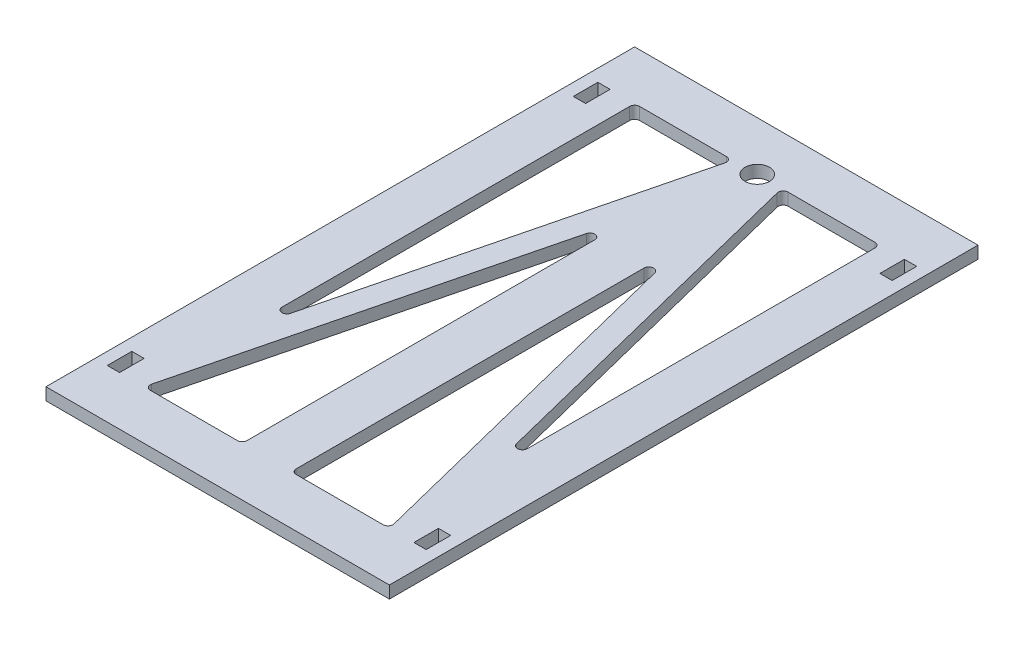
SolidWorks part; units mm, degrees
material "Beech"
ref_plane "Front Plane" through (0, 0, 0) normal (0, 0, 1) x (1, 0, 0)
ref_plane "Top Plane" through (0, 0, 0) normal (0, 1, 0) x (1, 0, 0)
ref_plane "Right Plane" through (0, 0, 0) normal (1, 0, 0) x (0, 0, -1)
sketch "Sketch1" plane through (0, 0, 0) normal (0, 1, 0) x (1, 0, 0)
  line L0 (0, 0) -> (177.8, 0)
  line L1 (0, 0) -> (0, 304.8)
  line L2 (177.8, 0) -> (177.8, 304.8)
  line L3 (0, 304.8) -> (177.8, 304.8)
  line L4 (0, 0) -> (12.7, 0)
  line L5 (0, 0) -> (0, -6.35)
  line L8 (177.8, 0) -> (165.1, 0)
  line L12 (127, 0) -> (114.3, 0)
  line L16 (50.8, 0) -> (63.5, 0)
  line L20 (165.1, 279.4) -> (171.45, 279.4)
  line L21 (165.1, 279.4) -> (165.1, 266.7)
  line L22 (171.45, 279.4) -> (171.45, 266.7)
  line L23 (165.1, 266.7) -> (171.45, 266.7)
  line L24 (6.35, 279.4) -> (12.7, 279.4)
  line L25 (6.35, 279.4) -> (6.35, 266.7)
  line L26 (12.7, 279.4) -> (12.7, 266.7)
  line L27 (6.35, 266.7) -> (12.7, 266.7)
  line L28 (6.35, 38.1) -> (12.7, 38.1)
  line L29 (6.35, 38.1) -> (6.35, 25.4)
  line L30 (12.7, 38.1) -> (12.7, 25.4)
  line L31 (6.35, 25.4) -> (12.7, 25.4)
  line L32 (165.1, 38.1) -> (171.45, 38.1)
  line L33 (165.1, 38.1) -> (165.1, 25.4)
  line L34 (171.45, 38.1) -> (171.45, 25.4)
  line L35 (165.1, 25.4) -> (171.45, 25.4)
  line L36 (101.6, 279.4) -> (152.4, 279.4)
  line L37 (152.4, 279.4) -> (152.4, 76.2)
  line L38 (152.4, 76.2) -> (101.6, 279.4)
  line L39 (101.6, 228.6) -> (101.6, 25.4)
  line L40 (101.6, 25.4) -> (152.4, 25.4)
  line L41 (152.4, 25.4) -> (101.6, 228.6)
  line L42 (76.2, 279.4) -> (25.4, 279.4)
  line L43 (25.4, 279.4) -> (25.4, 76.2)
  line L44 (25.4, 76.2) -> (76.2, 279.4)
  line L45 (76.2, 228.6) -> (76.2, 25.4)
  line L46 (76.2, 25.4) -> (25.4, 25.4)
  line L47 (25.4, 25.4) -> (76.2, 228.6)
  circle A0 centre (88.9, 279.4) radius 6.35
  point P21 (88.9, 304.8)
  dimension "D8" = 12.7
  dimension "D1" = 177.8
  dimension "D6" = 304.8
  dimension "D7" = 25.4
  dimension "D9" = 25.4
  dimension "D10" = 25.4
  dimension "D11" = 12.7
  dimension "D12" = 12.7
  dimension "D13" = 203.2
  dimension "D14" = 50.8
  dimension "D15" = 50.8
extrude "Front Panel" add sketch "Sketch1" along normal blind 6.35
fillet "Fillet1" radius 2.54 12 edges at (25.4, 3.175, -76.2) (152.4, 3.175, -76.2) (25.4, 3.175, -25.4) (76.2, 3.175, -25.4) (101.6, 3.175, -25.4) (152.4, 3.175, -25.4) (76.2, 3.175, -228.6) (101.6, 3.175, -228.6) (25.4, 3.175, -279.4) (76.2, 3.175, -279.4) (101.6, 3.175, -279.4) (152.4, 3.175, -279.4)
equation "\"CageLeftBottomEdge\"=22.11mm"
equation "\"CageLeftTopEdge\"=22.11mm"
equation "\"CageRightBottomEdge\"=21.63mm"
equation "\"CageRightTopEdge\"=21.63mm"
equation "\"CageHeight\"=86.04mm"
equation "\"CageLength\"=73.76mm"
equation "\"CageTopScrewClearance\"=10mm"
equation "\"CageBottomScrewClearance\"=25mm"
equation "\"CageLeftTopDepth\"= 11.65mm"
equation "\"CageLeftBottomDepth\"=11.11mm"
equation "\"CageLeftTopHeight\"=8.56175mm"
equation "\"CageLeftBottomHeight\"=16mm"
equation "\"CageRightTopDepth\"= 11.05mm"
equation "\"CageRightBottomDepth\"=10.58mm"
equation "\"CageRightTopHeight\"=9.6mm"
equation "\"CageRightBottomHeight\"=15.49mm"
equation "\"CageLeftTopChannelDepth\"=2.41908mm"
equation "\"CageLeftBottomChannelDepth\"=2.588mm"
equation "\"CageLeftChannelHeight\"=11.7mm"
equation "\"CageRightTopChannelDepth\"=2.32mm"
equation "\"CageRightBottomChannelDepth\"=2.318mm"
equation "\"CageRightChannelHeight\"=10mm"
equation "\"CageChanRelHeight\"=23.99mm"
equation "\"CageChanRelDepth\"=5.492mm"
equation "\"CageChamberRadius\"=16.261mm"
equation "\"CageScrewDiameter\"=4.8mm"
equation "\"CageSetScrewDiameter\"=3.5mm"
equation "\"CageAxleRadius\"=6.639mm"
equation "\"CageAxleKeyHeight\"=1.619mm"
equation "\"CageAxleKeyWidth\"=2.662mm"
equation "\"CageHoseWindowWidth\"=16.29mm"
equation "\"CageHoseWindowHeight\"=26.5mm"
equation "\"CageHoseWindow-Edge\"=8.89mm"
equation "\"CageScrew-VerticalEdge\"=5.0mm"
equation "\"CageScrew-HorizontalEdge\"=7.5mm"
equation "\"CageScrew-HoseCornerScrewEdge\"=4.45mm"
equation "\"CageAxle-BottomEdge\"=56.05mm"
equation "\"CageAxle-FrontEdge\"=46.03mm"
equation "\"CageBackSetScrew-Axle\"=40mm"
equation "\"CageFrontSetScrew-Axle\"=22mm"
equation "\"CageVelocityWindow-BackEdge\"=34.8mm"
equation "\"CageVelocityWindow-BottomEdge\"=27.55mm"
equation "\"CageVelocityWindowHeight\"=22.29mm"
equation "\"CageVelocityWindowWidth\"=12.61mm"
equation "\"TriggerSlot-BottomEdge\"=6.35mm"
equation "\"TriggerSlot-FrontEdge\"=15mm"
equation "\"TriggerSlotSize\"=6.7mm"
equation "\"TriggerRackOffset\"=6mm"
equation "\"TriggerSlotSizeInt\"=.25in"
equation "\"MotorMountLegLength\"=.25in"
equation "\"GearOffset\"=.264907in"
equation "\"TriggerSlotSpacing\"=.25in"
equation "\"TriggerMiniSlotWidth\"=3.5mm"
equation "\"TriggerRackWidth\"=6.5mm"
equation "\"pandiscradius\"=14in"
equation "\"towermaterialwidth\"=.25in"
equation "\"towerslotlength\"=.5in"
equation "\"towermarkerspace\"=5in"
equation "\"towerslothorizoffset\"=1in"
equation "\"towerslothorizspacing\"=2in"
equation "\"towerslotvertoffset\"=3in"
equation "\"towerslotvertspacing\"=1in"
equation "\"towerheight\"=12in"
equation "\"towerupslot\"=1in"
equation "\"D1@Sketch1\"=(\"towerslothorizoffset\"+\"towerslothorizspacing\"+\"towerslotlength\")*2"
equation "\"D2@Sketch1\"=\"towermaterialwidth\""
equation "\"D3@Sketch1\"=\"towerslotlength\""
equation "\"D4@Sketch1\"=\"towerslothorizspacing\""
equation "\"D5@Sketch1\"=\"towerslothorizspacing\""
equation "\"D6@Sketch1\"=\"towerheight\""
equation "\"D7@Sketch1\"=\"towerupslot\""
equation "\"toweraxle\"=.5in"
equation "\"D8@Sketch1\"= \"toweraxle\""
equation "\"D9@Sketch1\"=\"towerupslot\""
equation "\"D10@Sketch1\"= \"towerupslot\""
equation "\"D1@Front Panel\"=\"towermaterialwidth\""
equation "\"stepperouterrad\"=10mm"
equation "\"stepperscrewsize\"=3.45mm"
equation "\"stepperscrewc2c\"=49.5mm"
equation "\"stepperdepthoffset\"=24mm"
equation "\"stepperhorizoffset\"=22.91mm"
equation "\"shaftslotOD\"=18.8mm"
equation "\"shaftslotID\"=13.28mm"
equation "\"shaftkeywidth\"=2.67mm"
equation "\"shaftkeydepth\"=1.8mm"
equation "\"shaftcollartotaldepth\"=9.71mm"
equation "\"shaftsquaredepth\"=6mm"
equation "\"shaftsetscrewsize\"=3.5mm"
equation "\"shaftkeytightdepth\"=1.85mm"
equation "\"shaftslottightID\"=12.78mm"
equation "\"shaftsetscrewoffset\"=9mm"
equation "\"cagecollartotaldepth\"=20mm"
equation "\"cagecollartotalwidth\"=35mm"
equation "\"cagecollarbasedepth\"=4mm"
equation "\"D11@Sketch1\"=\"toweraxle\""
equation "\"D12@Sketch1\"=\"toweraxle\""
equation "\"towerspeedwidth\"=2in"
equation "\"D15@Sketch1\"=\"towerspeedwidth\""
equation "\"towerspeedheight\"=8in"
equation "\"D13@Sketch1\"=\"towerspeedheight\""
equation "\"towerspeedgap\"=2in"
equation "\"D14@Sketch1\"=\"towerspeedgap\""
equation "\"gearhubintdiam\"=30mm"
equation "\"gearhubintwid\"=12.21mm"
equation "\"stepperaxleflat\"=.037in"
equation "\"stepperaxlerad\"=0.11811024in"
equation "\"ajaxaxlesize\"=3.87mm"
equation "\"ajaxinnercut\"=2.3mm"
equation "\"ajaxwidth\"=6.1mm"
equation "\"ajaxdiametral\"=25.8854"
equation "\"ajaxcutoutdepth\"=2.3mm"
equation "\"ajax4020gap\"=29.5mm"
equation "\"ajax4010gap\"=24.5mm"
equation "\"ajax20hubbuffer\"=6.1mm"
equation "\"ajax20hubholeoffset\"=.19685in"
equation "\"ajax20hubholesize\"=.059055in"
equation "\"ajax20cutoutint\"=13.4mm"
equation "\"ajax40hubholesize\"=7.21mm"
equation "\"ajax40hubholeoffset\"=10mm"
equation "\"ajax40hubbuffer\"=8.9mm"
equation "\"ajax40cutoutint\"=32.6mm"
equation "\"bearingpandiscrad\"=6.8in"
equation "\"bearingpandiscang\"=48.75deg"
equation "\"bearingclearholedist\"=4.7345in"
equation "\"bearingclearholesize\"=.5in"
equation "\"bearingclearholeang\"=22.5deg"
equation "\"bearingmountholedist\"=4.25in"
equation "\"bearingwirehole\"=1.5in"
equation "\"no6diam\"=.146in"
equation "\"shortconangle\"=20deg"
equation "\"shortconlen\"=.875in"
equation "\"longconlen\"=1.25in"
equation "\"longconangle\"=15deg"
equation "\"D1@Fillet1\"= 0.1in"
equation "\"vigorwidth\"= 0.472441in"
equation "\"vigorflangewidth\"= 0.731102in"
equation "\"vigorflangelength\"= 0.131102in"
equation "\"vigorscrewsize\"= 0.066535in"
equation "\"vigorholeoffsetwid\"= 0.0646653in"
equation "\"vigorholeoffsetlen\"= 0.065551in"
equation "\"vigorflangedepth\"= 0.0901575in"
equation "\"vigordiscdepth\"= 0.0492126in"
equation "\"vigormotordepth\"= 1.12362in"
equation "\"vigortipdepth\"= 0.259055in"
equation "\"vigoraxlewidth\"= 0.173622in"
equation "\"vigorcutlen\"= 0.0480315in"
equation "\"vigoraxledepth\"= 0.159055in"
equation "\"BrassInsertDiameter\"=5.04mm"
